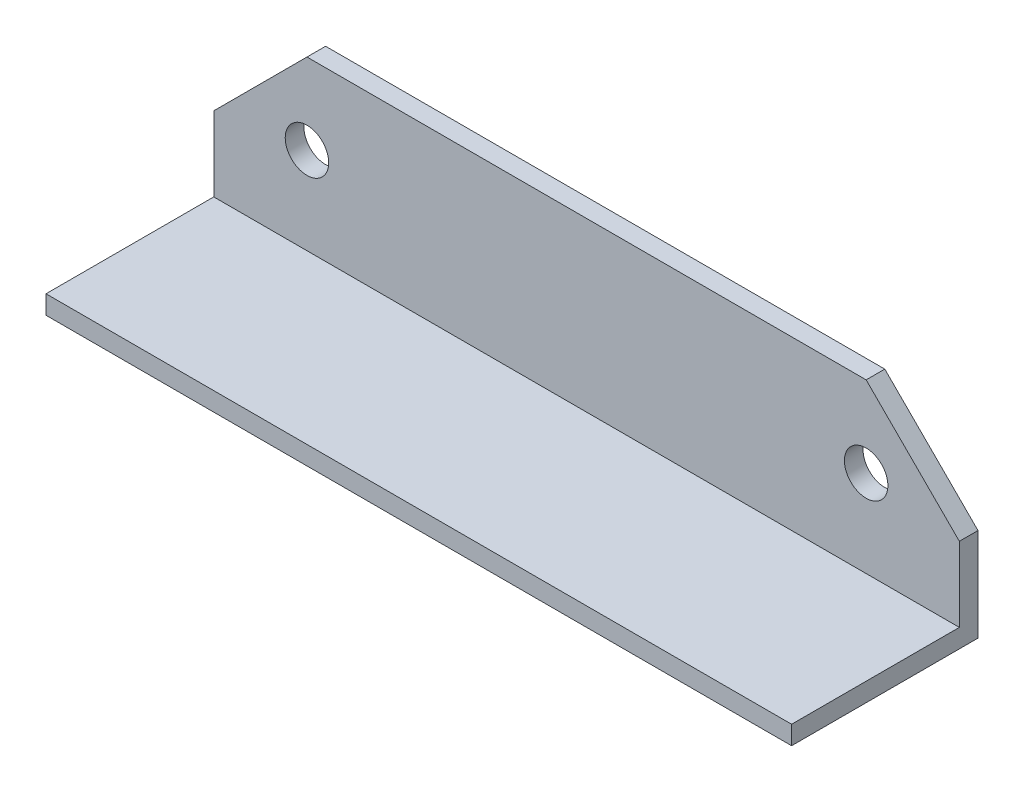
SolidWorks part; units mm, degrees
ref_plane "Alzado" through (0, 0, 0) normal (0, 0, 1) x (1, 0, 0)
ref_plane "Planta" through (0, 0, 0) normal (0, 1, 0) x (1, 0, 0)
ref_plane "Vista lateral" through (0, 0, 0) normal (1, 0, 0) x (0, 0, -1)
ref_plane "Plano1" through (0, 0, -77.1201) normal (0, 0, 1) x (1, 0, 0)
sketch "Croquis1" plane through (0, 0, -77.1201) normal (0, 0, 1) x (1, 0, 0)
  line L0 (-60, 662.65) -> (-60, 647.65)
  line L1 (-60, 647.65) -> (60, 647.65)
  line L2 (60, 647.65) -> (60, 662.65)
  line L3 (60, 662.65) -> (45, 677.65)
  line L4 (45, 677.65) -> (-45, 677.65)
  line L5 (-45, 677.65) -> (-60, 662.65)
extrude "Saliente-Extruir1" add sketch "Croquis1" against normal blind 3
sketch "Croquis2" plane through (0, 0, -77.1201) normal (0, 0, 1) x (1, 0, 0)
  line L0 (60, 650.65) -> (60, 647.65)
  line L1 (60, 647.65) -> (-60, 647.65)
  line L2 (-60, 647.65) -> (-60, 650.65)
  line L3 (-60, 650.65) -> (60, 650.65)
extrude "Saliente-Extruir2" add sketch "Croquis2" along normal blind 27
hole_wizard "Diámetro de taladro Ø7.0 (7)1" positions "Croquis4" profile "Croquis3" hole size "Ø7.0" standard "Ansi Metric"
sketch "Croquis4" plane through (0, 0, -80.1201) normal (0, 0, -1) x (-1, 0, 0)
  point P0 (45, 664.65)
  point P1 (-45, 664.65)
sketch "Croquis3" plane through (-45, 664.65, -80.1201) normal (1, 0, 0) x (0, 1, 0)
  line L0 (0, 0) -> (0, 30)
  line L1 (0, 30) -> (3.5, 30)
  line L2 (3.5, 30) -> (3.5, 0)
  line L5 (3.5, 0) -> (0, 0)
  line L11 (0, -6.35) -> (0, 107.95) construction
  dimension "Diámetro de taladro hasta el siguiente" = 7
  dimension "Profundidad de taladro hasta el siguiente" = 30
